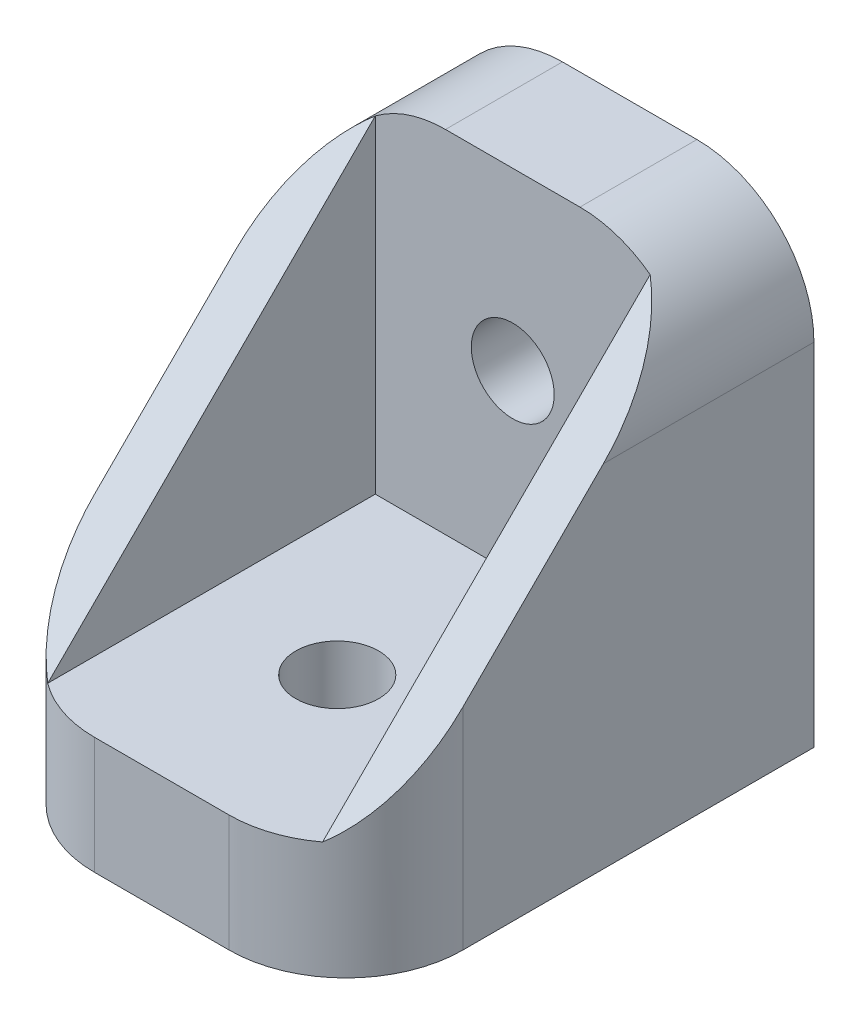
SolidWorks part; units mm, degrees
ref_plane "Front Plane" through (0, 0, 0) normal (0, 0, 1) x (1, 0, 0)
ref_plane "Top Plane" through (0, 0, 0) normal (0, 1, 0) x (1, 0, 0)
ref_plane "Right Plane" through (0, 0, 0) normal (1, 0, 0) x (0, 0, -1)
sketch "Sketch1" plane through (0, 0, 0) normal (1, 0, 0) x (0, 0, -1)
  line L0 (0, 0) -> (0, 6.35)
  line L1 (0, 6.35) -> (19.05, 6.35)
  line L2 (19.05, 6.35) -> (19.05, 25.4)
  line L3 (19.05, 25.4) -> (25.4, 25.4)
  line L4 (25.4, 25.4) -> (25.4, 0)
  line L5 (25.4, 0) -> (0, 0)
  dimension "D1" = 6.35
  dimension "D2" = 6.35
  dimension "D3" = 25.4
  dimension "D4" = 25.4
extrude "Boss-Extrude1" add sketch "Sketch1" along normal blind 20
sketch "Sketch2" plane through (0, 6.35, 0) normal (0, 1, 0) x (1, 0, 0)
  line L0 (0, 0) -> (20, 19.05)
  line L1 (0, 19.05) -> (20, 0)
  circle A0 centre (10, 9.525) radius 2.25
  dimension "D1" = 4.5
extrude "Cut-Extrude1" cut sketch "Sketch2" against normal blind 20 contours L0 A0 L1 | L1 A0 L0 | L0 A0 L1 | L1 A0 L0
sketch "Sketch3" plane through (0, 0, -19.05) normal (0, 0, 1) x (1, 0, 0)
  line L0 (0, 6.35) -> (20, 25.4)
  line L1 (0, 25.4) -> (20, 6.35)
  circle A0 centre (10, 15.875) radius 2.25
extrude "Cut-Extrude2" cut sketch "Sketch3" against normal blind 20 contours L1 A0 L0 | L0 A0 L1 | L1 A0 L0 | L0 A0 L1
fillet "Fillet1" radius 6.35 4 edges at (0, 3.175, 0) (20, 3.175, 0) (0, 25.4, -22.225) (20, 25.4, -22.225)
sketch "Sketch4" plane through (0, 6.35, 0) normal (0, 1, 0) x (1, 0, 0)
  line L0 (10, 19.05) -> (10, 0)
  line L1 (0, 19.05) -> (2.54, 19.05)
  line L2 (0, 19.05) -> (0, 6.35)
  line L4 (2.54, 19.05) -> (2.54, 1.27)
  line L5 (20, 19.05) -> (20, 6.35)
  line L6 (17.46, 19.05) -> (17.46, 1.27)
  line L7 (20, 19.05) -> (20, 6.35)
  line L8 (0, 19.05) -> (0, 6.35)
  line L9 (6.35, 0) -> (13.65, 0)
  line L10 (20, 6.35) -> (20, 19.05)
  line L11 (20, 19.05) -> (0, 19.05)
  line L12 (0, 19.05) -> (0, 6.35)
  line L13 (6.35, 0) -> (13.65, 0)
  line L14 (20, 6.35) -> (20, 19.05)
  line L15 (20, 19.05) -> (0, 19.05)
  line L16 (20, 19.05) -> (17.46, 19.05)
  arc A2 (0, 6.35) -> (6.35, 0) centre (6.35, 6.35) ccw
  arc A3 (13.65, 0) -> (20, 6.35) centre (13.65, 6.35) ccw
  arc A4 (0, 6.35) -> (6.35, 0) centre (6.35, 6.35) ccw
  arc A5 (13.65, 0) -> (20, 6.35) centre (13.65, 6.35) ccw
  line M12 (0, 19.05) -> (0, 6.35)
  arc M13 (0, 6.35) -> (6.35, 0) centre (6.35, 6.35) ccw
  arc M15 (13.65, 0) -> (20, 6.35) centre (13.65, 6.35) ccw
  line M16 (20, 6.35) -> (20, 19.05)
  line M17 (20, 19.05) -> (0, 19.05)
  dimension "D1" = 2.54
  dimension "D2" = 0
extrude "Boss-Extrude2" add sketch "Sketch4" along normal up to surface (19.05 mm away) contours L4 M17 M12 M13 | L6 M17 M15 M16 up to face at (10, 25.4, -22.225)
sketch "Sketch5" plane through (0, 0, -19.05) normal (0, 0, -1) x (-1, 0, 0)
  line L3 (0, 19.05) -> (0, 25.4)
  line L4 (0, 25.4) -> (-2.54, 25.4)
  line L5 (-2.54, 25.4) -> (-2.54, 24.13)
  line L6 (0, 19.05) -> (0, 25.4)
  line L7 (0, 25.4) -> (-2.54, 25.4)
  line L8 (-2.54, 25.4) -> (-2.54, 24.13)
  line L9 (-17.46, 24.13) -> (-17.46, 25.4)
  line L10 (-17.46, 25.4) -> (-20, 25.4)
  line L11 (-20, 25.4) -> (-20, 19.05)
  line L12 (-17.46, 24.13) -> (-17.46, 25.4)
  line L13 (-17.46, 25.4) -> (-20, 25.4)
  line L14 (-20, 25.4) -> (-20, 19.05)
  arc A1 (0, 19.05) -> (-2.54, 24.13) centre (-6.35, 19.05) ccw
  arc A2 (0, 19.05) -> (-2.54, 24.13) centre (-6.35, 19.05) ccw
  arc A3 (-17.46, 24.13) -> (-20, 19.05) centre (-13.65, 19.05) ccw
  arc A4 (-17.46, 24.13) -> (-20, 19.05) centre (-13.65, 19.05) ccw
  dimension "D1" = 0
  dimension "D2" = 0
extrude "Cut-Extrude3" cut sketch "Sketch5" against normal through all
sketch "Sketch6" plane through (0, 0, 0) normal (-1, 0, 0) x (0, 0, 1)
  line L0 (-6.35, 19.05) -> (-6.35, 0) construction
  line L1 (-6.35, 0) -> (0, 0) construction
  line L2 (0, 0) -> (0, 6.35) construction
  line L3 (0, 6.35) -> (-1.27, 6.35) construction
  line L4 (-1.27, 6.35) -> (-1.27, 24.13) construction
  line L5 (-25.4, 25.4) -> (-25.4, 19.05) construction
  line L6 (-25.4, 19.05) -> (-6.35, 19.05) construction
  line L7 (-1.27, 24.13) -> (-19.05, 24.13) construction
  line L8 (-19.05, 24.13) -> (-19.05, 25.4) construction
  line L9 (-19.05, 25.4) -> (-25.4, 25.4) construction
  line L10 (-6.35, 19.05) -> (-6.35, 0)
  line L11 (-6.35, 0) -> (0, 0)
  line L12 (0, 0) -> (0, 6.35)
  line L13 (0, 6.35) -> (-1.27, 6.35)
  line L14 (-1.27, 6.35) -> (-1.27, 24.13)
  line L15 (-25.4, 25.4) -> (-25.4, 19.05)
  line L16 (-25.4, 19.05) -> (-6.35, 19.05)
  line L17 (-1.27, 24.13) -> (-19.05, 24.13)
  line L18 (-19.05, 24.13) -> (-19.05, 25.4)
  line L19 (-19.05, 25.4) -> (-25.4, 25.4)
  line L20 (-19.05, 24.13) -> (-1.27, 6.35)
  line M2 (-6.35, 19.05) -> (-25.4, 19.05)
extrude "Cut-Extrude4" cut sketch "Sketch6" against normal through all contours L17 L20 L10 L14 M2 | L20 L10 M2
